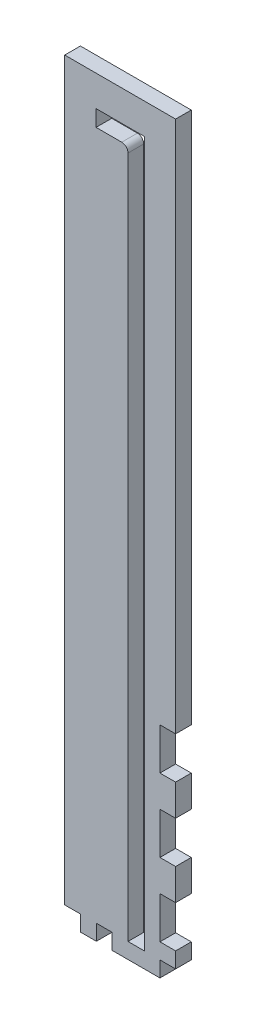
SolidWorks part; units mm, degrees
material "Acrylic (Medium-high impact)"
ref_plane "Front" through (0, 0, 0) normal (0, 0, 1) x (1, 0, 0)
ref_plane "Top" through (0, 0, 0) normal (0, 1, 0) x (1, 0, 0)
ref_plane "Right" through (0, 0, 0) normal (1, 0, 0) x (0, 0, -1)
sketch "Sketch1" plane through (0, 0, 0) normal (0, 0, 1) x (1, 0, 0)
  line L0 (0, 143.002) -> (0, -143.002) construction
  line L1 (-3.302, 133.858) -> (-3.302, -143.002)
  line L2 (-3.302, -143.002) -> (3.302, -143.002)
  line L3 (3.302, 143.002) -> (3.302, -143.002)
  line L4 (3.302, 143.002) -> (-16.256, 143.002)
  line L5 (-5.842, 136.398) -> (-16.256, 136.398)
  line L6 (-16.256, 143.002) -> (-16.256, 136.398)
  line L8 (-28.956, 155.448) -> (16.002, 155.448)
  line L9 (-28.956, 155.448) -> (-28.956, -149.352)
  line L10 (-28.956, -149.352) -> (16.002, -149.352)
  line L11 (16.002, 155.448) -> (16.002, -149.352)
  arc A0 (-3.302, 133.858) -> (-5.842, 136.398) centre (-5.842, 133.858) ccw
  point P2 (0, -143.002)
  point P11 (0, 0)
  dimension "D5" = 2.54
  dimension "D1" = 6.604
  dimension "D2" = 12.954
  dimension "D3" = 6.604
  dimension "D4" = 286.004
  dimension "D6" = 304.8
  dimension "D7" = 6.35
  dimension "D8" = 12.7
  dimension "D9" = 12.7
extrude "Boss-Extrude1" add sketch "Sketch1" along normal blind 6.35
sketch "Sketch2" plane through (16.002, 0, 0) normal (1, 0, 0) x (0, 0, -1)
  line L0 (-6.35, -149.352) -> (-6.35, 155.448) construction
  line L1 (-6.35, -47.752) -> (228.6, -47.752)
  line L2 (-6.35, -47.752) -> (-6.35, -149.352)
  line L3 (-6.35, -149.352) -> (228.6, -149.352)
  line L4 (228.6, -47.752) -> (228.6, -149.352)
  line L5 (14.4, -101.092) -> (14.4, -96.012)
  line L6 (36.4, -96.012) -> (36.4, -101.092)
  line L7 (8.4, -116.592) -> (8.4, -111.512)
  line L8 (11.4, -116.592) -> (11.4, -111.512)
  line L9 (8.4, -85.592) -> (8.4, -80.512)
  line L10 (11.4, -85.592) -> (11.4, -80.512)
  line L11 (25.4, -96.012) -> (25.4, -101.092) construction
  line L12 (42.4, -116.592) -> (42.4, -111.512)
  line L13 (39.4, -116.592) -> (39.4, -111.512)
  line L14 (39.4, -85.592) -> (39.4, -80.512)
  line L15 (42.4, -85.592) -> (42.4, -80.512)
  line L16 (0, -149.352) -> (0, 155.448) construction
  line L17 (225.425, -60.452) -> (225.425, -77.3853) construction
  line L18 (228.6, -47.752) -> (222.25, -47.752)
  line L19 (228.6, -47.752) -> (228.6, -60.452)
  line L20 (228.6, -60.452) -> (222.25, -60.452)
  line L21 (222.25, -47.752) -> (222.25, -60.452)
  line L22 (228.6, -107.0187) -> (222.25, -107.0187)
  line L23 (228.6, -107.0187) -> (228.6, -119.7187)
  line L24 (228.6, -119.7187) -> (222.25, -119.7187)
  line L25 (222.25, -107.0187) -> (222.25, -119.7187)
  line L26 (228.6, -136.652) -> (222.25, -136.652)
  line L27 (228.6, -136.652) -> (228.6, -149.352)
  line L28 (228.6, -149.352) -> (222.25, -149.352)
  line L29 (222.25, -136.652) -> (222.25, -149.352)
  line L30 (228.6, -77.3853) -> (222.25, -77.3853)
  line L31 (228.6, -77.3853) -> (228.6, -90.0853)
  line L32 (228.6, -90.0853) -> (222.25, -90.0853)
  line L33 (222.25, -77.3853) -> (222.25, -90.0853)
  line L34 (225.425, -90.0853) -> (225.425, -107.0187) construction
  line L35 (225.425, -119.7187) -> (225.425, -136.652) construction
  arc A0 (14.4, -101.092) -> (36.4, -101.092) centre (25.4, -101.092) ccw
  arc A1 (36.4, -96.012) -> (14.4, -96.012) centre (25.4, -96.012) ccw
  arc A2 (8.4, -116.592) -> (11.4, -116.592) centre (9.9, -116.592) ccw
  arc A3 (11.4, -111.512) -> (8.4, -111.512) centre (9.9, -111.512) ccw
  arc A4 (8.4, -85.592) -> (11.4, -85.592) centre (9.9, -85.592) ccw
  arc A5 (11.4, -80.512) -> (8.4, -80.512) centre (9.9, -80.512) ccw
  arc A6 (42.4, -116.592) -> (39.4, -116.592) centre (40.9, -116.592) cw
  arc A7 (39.4, -111.512) -> (42.4, -111.512) centre (40.9, -111.512) cw
  arc A8 (42.4, -85.592) -> (39.4, -85.592) centre (40.9, -85.592) cw
  arc A9 (39.4, -80.512) -> (42.4, -80.512) centre (40.9, -80.512) cw
  point P44 (25.4, -98.552)
  point P47 (-6.35, -98.552)
  line M17 (0, -149.352) -> (0, 155.448)
  line M19 (-6.35, 155.448) -> (-6.35, -149.352)
  line M20 (-6.35, -149.352) -> (0, -149.352)
  dimension "D1" = 22
  dimension "D6" = 1.5
  dimension "D10" = 1.5
  dimension "D2" = 5.08
  dimension "D3" = 5.08
  dimension "D4" = 15.5
  dimension "D5" = 15.5
  dimension "D7" = 15.5
  dimension "D8" = 15.5
  dimension "D9" = 5.08
  dimension "D11" = 25.4
  dimension "D12" = 50.8
  dimension "D13" = 203.2
  dimension "D14" = 12.7
  dimension "D15" = 6.35
extrude "Boss-Extrude2" add sketch "Sketch2" against normal blind 6.35 contours L33 L30 L4 L20 L21 L1 L3 L29 L26 L24 L25 L22 L32 A5 L10 A4 L9 A3 L8 A2 L7 A1 L6 A0 L5 L13 A7 L12 A6 L14 A9 L15 A8 M17 | L1 M19 M20 M17
sketch "Sketch3" plane through (9.652, 0, 0) normal (-1, 0, 0) x (0, 0, 1)
  line L0 (-222.25, -136.652) -> (-222.25, -149.352) construction
  line L1 (-222.25, -143.002) -> (0, -143.002)
  line L2 (-222.25, -143.002) -> (-222.25, -149.352)
  line L3 (-222.25, -149.352) -> (0, -149.352)
  line L4 (0, -143.002) -> (0, -149.352)
  dimension "D1" = 6.35
extrude "Boss-Extrude3" add sketch "Sketch3" along normal up to surface (38.608 mm away) up to face at (-28.956, 3.048, 3.175)
sketch "Sketch4" plane through (0, -149.352, 0) normal (0, -1, 0) x (1, 0, 0)
  line L0 (9.652, -20.6375) -> (9.652, -33.3375)
  line L1 (16.002, 6.35) -> (9.652, 6.35)
  line L2 (16.002, 6.35) -> (16.002, -6.35)
  line L3 (16.002, -6.35) -> (9.652, -6.35)
  line L4 (9.652, 6.35) -> (9.652, -6.35)
  line L5 (16.002, -20.6375) -> (9.652, -20.6375)
  line L6 (16.002, -20.6375) -> (16.002, -33.3375)
  line L7 (16.002, -33.3375) -> (9.652, -33.3375)
  line L8 (9.652, -47.625) -> (9.652, -60.325)
  line L9 (16.002, -47.625) -> (9.652, -47.625)
  line L10 (16.002, -47.625) -> (16.002, -60.325)
  line L11 (16.002, -60.325) -> (9.652, -60.325)
  line L12 (9.652, -74.6125) -> (9.652, -87.3125)
  line L13 (16.002, -74.6125) -> (9.652, -74.6125)
  line L14 (16.002, -74.6125) -> (16.002, -87.3125)
  line L15 (16.002, -87.3125) -> (9.652, -87.3125)
  line L16 (9.652, -101.6) -> (9.652, -114.3)
  line L17 (16.002, -101.6) -> (9.652, -101.6)
  line L18 (16.002, -101.6) -> (16.002, -114.3)
  line L19 (16.002, -114.3) -> (9.652, -114.3)
  line L20 (9.652, -128.5875) -> (9.652, -141.2875)
  line L21 (16.002, -128.5875) -> (9.652, -128.5875)
  line L22 (16.002, -128.5875) -> (16.002, -141.2875)
  line L23 (16.002, -141.2875) -> (9.652, -141.2875)
  line L24 (9.652, -155.575) -> (9.652, -168.275)
  line L25 (16.002, -155.575) -> (9.652, -155.575)
  line L26 (16.002, -155.575) -> (16.002, -168.275)
  line L27 (16.002, -168.275) -> (9.652, -168.275)
  line L28 (9.652, -182.5625) -> (9.652, -195.2625)
  line L29 (16.002, -182.5625) -> (9.652, -182.5625)
  line L30 (16.002, -182.5625) -> (16.002, -195.2625)
  line L31 (16.002, -195.2625) -> (9.652, -195.2625)
  line L32 (9.652, -209.55) -> (9.652, -222.25)
  line L33 (16.002, -209.55) -> (9.652, -209.55)
  line L34 (16.002, -209.55) -> (16.002, -222.25)
  line L35 (16.002, -222.25) -> (9.652, -222.25)
  line L36 (-6.477, 6.35) -> (-6.477, -222.25) construction
  line L37 (-28.956, 6.35) -> (16.002, 6.35) construction
  line L38 (-28.956, -222.25) -> (16.002, -222.25) construction
  line L39 (-22.606, 6.35) -> (-22.606, -222.25)
  line L40 (16.002, 6.35) -> (9.652, 6.35)
  line L41 (16.002, 6.35) -> (16.002, -222.25)
  line L42 (16.002, -222.25) -> (9.652, -222.25)
  line L43 (9.652, 6.35) -> (9.652, -222.25)
  line L44 (-28.956, -222.25) -> (-22.606, -222.25)
  line L45 (-28.956, 6.35) -> (-28.956, -222.25)
  line L46 (-28.956, 6.35) -> (-22.606, 6.35)
  line L47 (-28.956, -222.25) -> (-22.606, -222.25)
  line L48 (-28.956, -209.55) -> (-28.956, -222.25)
  line L49 (-28.956, -209.55) -> (-22.606, -209.55)
  line L50 (-22.606, -209.55) -> (-22.606, -222.25)
  line L51 (-28.956, -195.2625) -> (-22.606, -195.2625)
  line L52 (-28.956, -182.5625) -> (-28.956, -195.2625)
  line L53 (-28.956, -182.5625) -> (-22.606, -182.5625)
  line L54 (-22.606, -182.5625) -> (-22.606, -195.2625)
  line L55 (-28.956, -168.275) -> (-22.606, -168.275)
  line L56 (-28.956, -155.575) -> (-28.956, -168.275)
  line L57 (-28.956, -155.575) -> (-22.606, -155.575)
  line L58 (-22.606, -155.575) -> (-22.606, -168.275)
  line L59 (-28.956, -141.2875) -> (-22.606, -141.2875)
  line L60 (-28.956, -128.5875) -> (-28.956, -141.2875)
  line L61 (-28.956, -128.5875) -> (-22.606, -128.5875)
  line L62 (-22.606, -128.5875) -> (-22.606, -141.2875)
  line L63 (-28.956, -114.3) -> (-22.606, -114.3)
  line L64 (-28.956, -101.6) -> (-28.956, -114.3)
  line L65 (-28.956, -101.6) -> (-22.606, -101.6)
  line L66 (-22.606, -101.6) -> (-22.606, -114.3)
  line L67 (-28.956, -87.3125) -> (-22.606, -87.3125)
  line L68 (-28.956, -74.6125) -> (-28.956, -87.3125)
  line L69 (-28.956, -74.6125) -> (-22.606, -74.6125)
  line L70 (-22.606, -74.6125) -> (-22.606, -87.3125)
  line L71 (-28.956, -60.325) -> (-22.606, -60.325)
  line L72 (-28.956, -47.625) -> (-28.956, -60.325)
  line L73 (-28.956, -47.625) -> (-22.606, -47.625)
  line L74 (-22.606, -47.625) -> (-22.606, -60.325)
  line L75 (-28.956, -33.3375) -> (-22.606, -33.3375)
  line L76 (-28.956, -20.6375) -> (-28.956, -33.3375)
  line L77 (-28.956, -20.6375) -> (-22.606, -20.6375)
  line L78 (-22.606, 6.35) -> (-22.606, -6.35)
  line L79 (-28.956, -6.35) -> (-22.606, -6.35)
  line L80 (-28.956, 6.35) -> (-28.956, -6.35)
  line L81 (-28.956, 6.35) -> (-22.606, 6.35)
  line L82 (-22.606, -20.6375) -> (-22.606, -33.3375)
  line L83 (-16.129, 3.175) -> (-22.606, 3.175) construction
  line L85 (-28.956, 6.35) -> (-22.606, 6.35)
  line L86 (-28.956, 6.35) -> (-28.956, 0)
  line L87 (-28.956, 0) -> (-22.606, 0)
  line L88 (-22.606, 6.35) -> (-22.606, 0)
  line L92 (9.652, 6.35) -> (9.652, 0)
  line L93 (9.652, 6.35) -> (16.002, 6.35)
  line L94 (16.002, 6.35) -> (16.002, 0)
  line L95 (9.652, 0) -> (16.002, 0)
  line L96 (-28.956, 6.35) -> (16.002, 6.35)
  line L97 (-28.956, 6.35) -> (-28.956, 0)
  line L98 (-28.956, 0) -> (16.002, 0)
  line L99 (16.002, 6.35) -> (16.002, 0)
  line L100 (-9.652, 6.35) -> (-9.652, 0) [skipped]
  line L101 (-9.652, 0) -> (-3.302, 0) [skipped]
  line L102 (-3.302, 6.35) -> (-3.302, 0) [skipped]
  line L103 (-9.652, 6.35) -> (-3.302, 6.35) [skipped]
  line L104 (-9.779, 0) -> (-16.129, 0)
  line L105 (-9.779, 0) -> (-9.779, 6.35)
  line L106 (-9.779, 6.35) -> (-16.129, 6.35)
  line L107 (-16.129, 0) -> (-16.129, 6.35)
  line L108 (-9.779, 3.175) -> (-3.302, 3.175) construction
  line L109 (-3.302, 6.35) -> (-3.302, 0) construction
  line M39 (16.002, 6.35) -> (-28.956, 6.35)
  line M40 (-28.956, 6.35) -> (-28.956, -222.25)
  dimension "D1" = 6.35
  dimension "D2" = 12.7
  dimension "D4" = 6.35
  dimension "D5" = 6.35
  dimension "D7" = 6.35
  dimension "D3" = 9
  dimension "D6" = 3
sketch "Sketch6" plane through (0, 0, 6.35) normal (0, 0, 1) x (1, 0, 0)
  line L0 (16.002, -136.652) -> (16.002, -149.352) construction
  line L1 (16.002, -60.452) -> (9.652, -60.452)
  line L2 (16.002, -60.452) -> (16.002, -77.3853)
  line L3 (16.002, -77.3853) -> (9.652, -77.3853)
  line L4 (9.652, -60.452) -> (9.652, -77.3853)
  line L5 (16.002, -90.0853) -> (9.652, -90.0853)
  line L6 (16.002, -90.0853) -> (16.002, -107.0187)
  line L7 (16.002, -107.0187) -> (9.652, -107.0187)
  line L8 (9.652, -90.0853) -> (9.652, -107.0187)
  line L9 (16.002, -119.7187) -> (9.652, -119.7187)
  line L10 (16.002, -119.7187) -> (16.002, -136.652)
  line L11 (16.002, -136.652) -> (9.652, -136.652)
  line L12 (9.652, -119.7187) -> (9.652, -136.652)
sketch "Sketch7" plane through (16.002, 0, 0) normal (1, 0, 0) x (0, 0, -1)
  line L0 (0, -47.752) -> (0, 155.448) construction
  line L1 (0, -8.6302) -> (327.0227, -8.6302)
  line L2 (0, -8.6302) -> (0, -288.0659)
  line L3 (0, -288.0659) -> (327.0227, -288.0659)
  line L4 (327.0227, -8.6302) -> (327.0227, -288.0659)
extrude "Cut-Extrude1" cut sketch "Sketch7" against normal through all
extrude "Cut-Extrude2" cut sketch "Sketch4" against normal blind 6.35 contours L107 L98 L105 L96 | L4 L95 L41 M39 | L87 L39 M40 M39 | L20 L23 L22 L21 | L10 L11 L8 L9 | L24 L27 L26 L25
extrude "Cut-Extrude3" cut sketch "Sketch6" against normal through all
